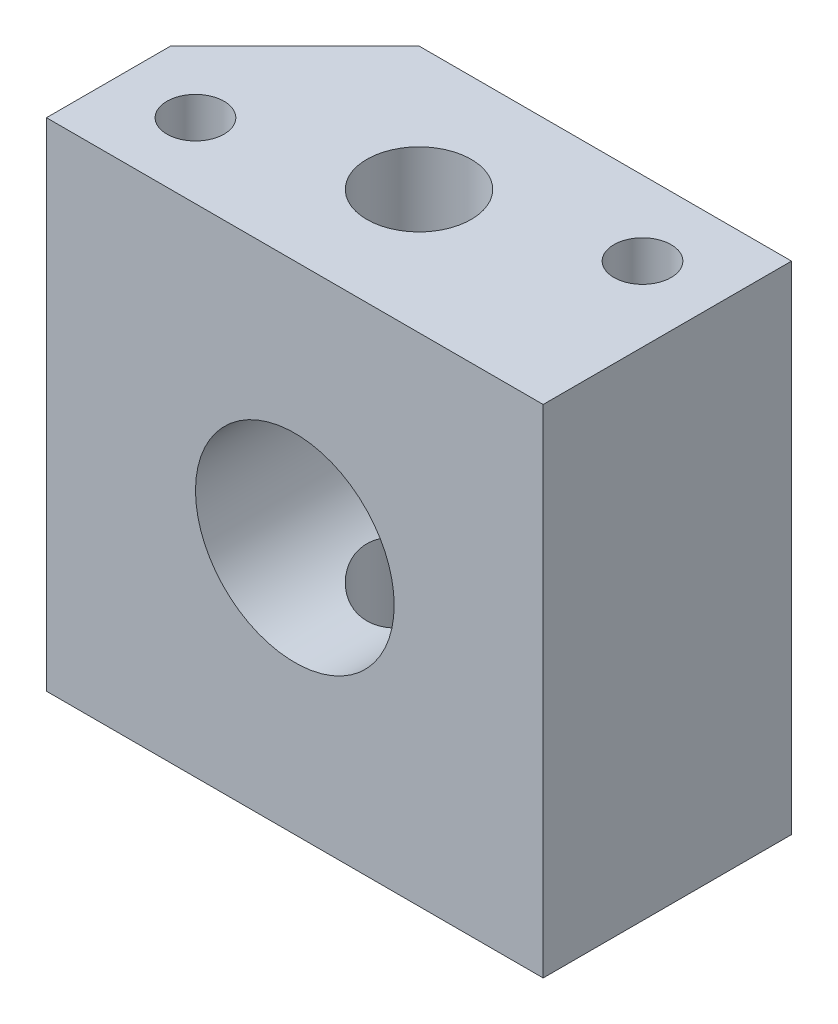
SolidWorks part; units mm, degrees
material "1060 Alloy"
ref_plane "Front Plane" through (0, 0, 0) normal (0, 0, 1) x (1, 0, 0)
ref_plane "Top Plane" through (0, 0, 0) normal (0, 1, 0) x (1, 0, 0)
ref_plane "Right Plane" through (0, 0, 0) normal (1, 0, 0) x (0, 0, -1)
sketch "Sketch1" plane through (0, 0, 0) normal (0, 0, 1) x (1, 0, 0)
  line L1 (0, 0) -> (20, 0)
  line L2 (0, 0) -> (0, 20)
  line L3 (0, 20) -> (20, 20)
  line L4 (20, 0) -> (20, 20)
  circle A0 centre (10, 10) radius 4
  dimension "D3" = 8
  dimension "D1" = 20
  dimension "D2" = 20
  dimension "D4" = 10
  dimension "D5" = 10
extrude "Boss-Extrude1" add sketch "Sketch1" along normal blind 10
sketch "Sketch2" plane through (0, 20, 0) normal (0, 1, 0) x (1, 0, 0)
  line L0 (20, -10) -> (0, -10) construction
  line L1 (0, -10) -> (0, 0) construction
  line L2 (20, -10) -> (20, 0) construction
  line L3 (20, 0) -> (0, 0) construction
  circle A0 centre (3, -7) radius 1.15
  circle A1 centre (17, -3) radius 1.15
  circle A2 centre (10, -5) radius 2.1
  dimension "D1" = 4.2
  dimension "D2" = 2.3
  dimension "D3" = 3
  dimension "D4" = 3
  dimension "D5" = 3
  dimension "D6" = 3
  dimension "D7" = 10
  dimension "D8" = 5
extrude "Cut-Extrude1" cut sketch "Sketch2" against normal through all
chamfer "Chamfer1" distance 5 angle 45 1 edges at (0, 10, 0)
